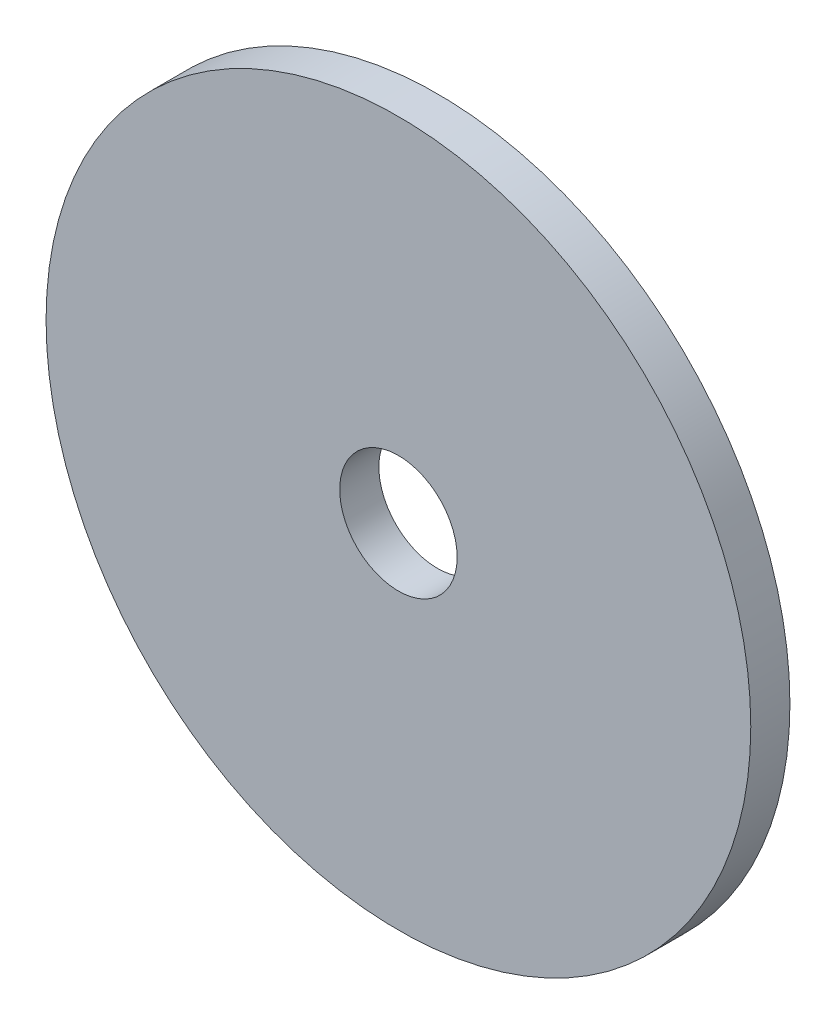
SolidWorks part; units mm, degrees
material "6061 Alloy"
ref_plane "Front Plane" through (0, 0, 0) normal (0, 0, 1) x (1, 0, 0)
ref_plane "Top Plane" through (0, 0, 0) normal (0, 1, 0) x (1, 0, 0)
ref_plane "Right Plane" through (0, 0, 0) normal (1, 0, 0) x (0, 0, -1)
sketch "Sketch1" plane through (0, 0, 0) normal (0, 0, 1) x (1, 0, 0)
  circle A0 centre (0, 0) radius 3
  circle A1 centre (0, 0) radius 18
  dimension "D1" = 6
  dimension "D2" = 36
extrude "Boss-Extrude1" add sketch "Sketch1" along normal blind 2
